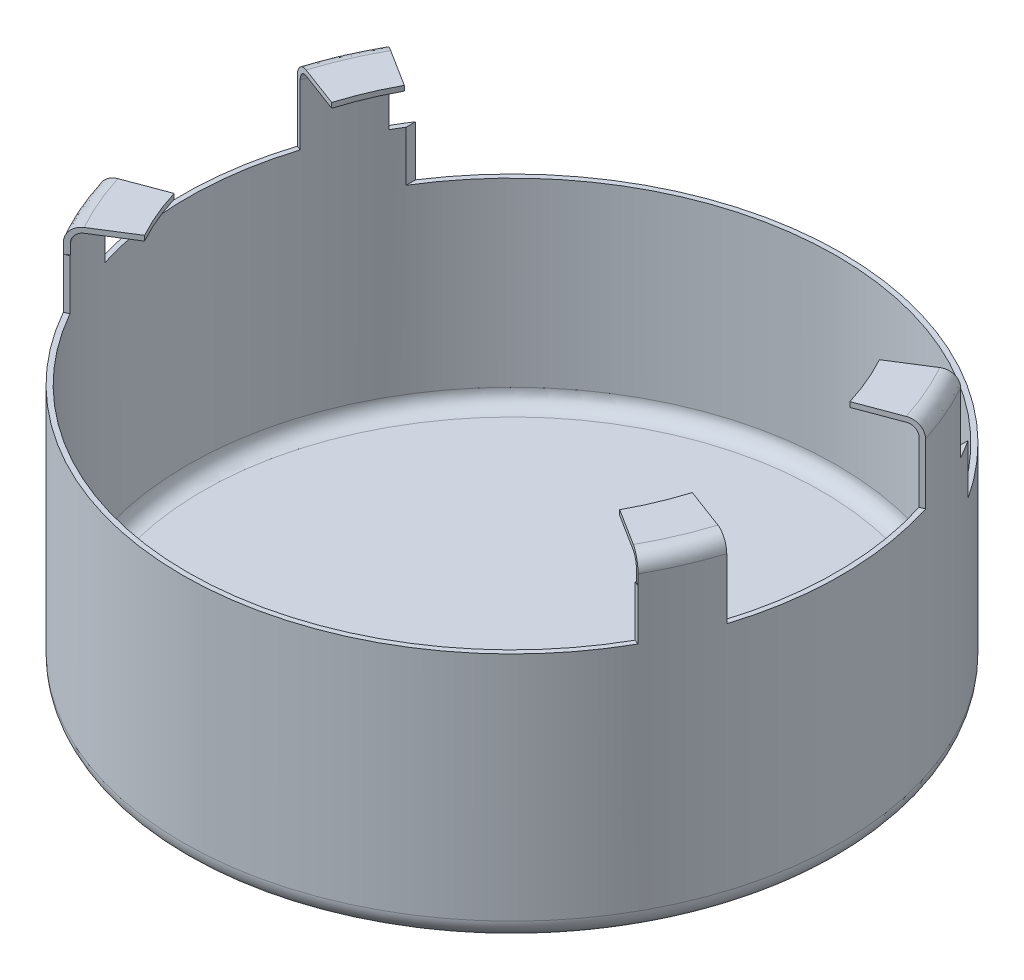
SolidWorks part; units mm, degrees
other "DetailItem6"
ref_plane "Front" through (0, 0, 0) normal (0, 0, 1) x (1, 0, 0)
ref_plane "Top" through (0, 0, 0) normal (0, 1, 0) x (1, 0, 0)
ref_plane "Right" through (0, 0, 0) normal (1, 0, 0) x (0, 0, -1)
sketch "Sketch1" plane through (0, 0, 0) normal (0, 1, 0) x (1, 0, 0)
  circle A0 centre (0, 0) radius 8.3185
extrude "Boss-Extrude1" add sketch "Sketch1" along normal blind 6.35
fillet "Fillet1" radius 0.508 1 edges at (0, 0, 8.3185)
shell "Shell1" thickness 0.127
sketch "Sketch11" plane through (0, 0, 0) normal (0, 0, 1) x (1, 0, 0)
  line L0 (8.3185, 6.35) -> (-8.3185, 6.35) construction
  line L1 (-6.9728, 5.08) -> (6.9728, 5.08)
  line L2 (-6.9728, 5.08) -> (-6.9728, 10.4572)
  line L3 (-6.9728, 10.4572) -> (6.9728, 10.4572)
  line L4 (6.9728, 5.08) -> (6.9728, 10.4572)
  line L5 (-6.9728, 5.08) -> (6.9728, 10.4572) construction
  line L6 (-6.9728, 10.4572) -> (6.9728, 5.08) construction
  point P0 (0, 7.7686)
  dimension "D1" = 1.27
extrude "Cut-Extrude1" cut sketch "Sketch11" against normal blind 9.144
sketch "Sketch12" plane through (0, 6.35, 0) normal (0, 1, 0) x (1, 0, 0)
  line L0 (0, 0) -> (0, 5.2829) construction
  line L1 (-7.1334, 4.0268) -> (-7.2538, 4.0718)
  line L2 (-7.8118, 2.465) -> (-7.9309, 2.5096)
  line L3 (0, 0) -> (4.1266, 0) construction
  line L4 (7.8118, 2.465) -> (7.9309, 2.5096)
  line L5 (7.1334, 4.0268) -> (7.2538, 4.0718)
  line L6 (7.1334, -4.0268) -> (7.2538, -4.0718)
  line L7 (7.8118, -2.465) -> (7.9309, -2.5096)
  line L8 (-7.8118, -2.465) -> (-7.9309, -2.5096)
  line L9 (-7.1334, -4.0268) -> (-7.2538, -4.0718)
  arc A0 (-6.9728, 4.5362) -> (6.9728, 4.5362) centre (0, 0) ccw construction
  arc A1 (-7.2538, 4.0718) -> (-7.9309, 2.5096) centre (0, 0) ccw
  circle A2 centre (0, 0) radius 8.1915 construction
  arc A3 (-7.1334, 4.0268) -> (-7.8118, 2.465) centre (0, 0) ccw
  arc A4 (7.1334, 4.0268) -> (7.8118, 2.465) centre (0, 0) cw
  arc A5 (7.2538, 4.0718) -> (7.9309, 2.5096) centre (0, 0) cw
  arc A6 (7.2538, -4.0718) -> (7.9309, -2.5096) centre (0, 0) ccw
  arc A7 (7.1334, -4.0268) -> (7.8118, -2.465) centre (0, 0) ccw
  arc A8 (-7.1334, -4.0268) -> (-7.8118, -2.465) centre (0, 0) cw
  arc A9 (-7.2538, -4.0718) -> (-7.9309, -2.5096) centre (0, 0) cw
extrude "Boss-Extrude2" add sketch "Sketch12" along normal blind 1.27
sketch "Sketch13" plane through (-0.151, 0, 0.4032) normal (-0.3506, 0, 0.9365) x (0.9365, 0, 0.3506)
  line L0 (-8.1802, 7.62) -> (-8.1802, 7.8808)
  line L1 (-7.9262, 8.1348) -> (-6.8225, 8.1348)
  line L2 (-6.8225, 8.1348) -> (-6.8225, 8.2618)
  line L3 (-6.8225, 8.2618) -> (-7.9264, 8.2618)
  line L4 (-8.3074, 7.62) -> (-8.3074, 7.8808)
  line L5 (-8.3074, 7.62) -> (-8.1802, 7.62)
  arc A0 (-8.1802, 7.8808) -> (-7.9262, 8.1348) centre (-7.9262, 7.8808) cw
  arc A1 (-8.3074, 7.8808) -> (-7.9264, 8.2618) centre (-7.9264, 7.8808) cw
  dimension "D1" = 0.254
  dimension "D2" = 0.381
  dimension "D3" = 0.127
sketch3d "3DSketch2"
  arc A0 (-7.2538, 7.62, -4.0718) -> (-7.9309, 7.62, -2.5096) centre (0, 7.62, 0) ccw construction
  arc A1 (-7.2538, 7.62, -4.0718) -> (-7.9309, 7.62, -2.5096) centre (0, 7.62, 0) ccw
  point P3 (0, 15.9385, 0)
  point P4 (0, 15.9385, 0)
sweep "Sweep1" add profiles "Sketch13" path "3DSketch2"
mirror "Mirror1" about plane through (0, 0, 0) normal (1, 0, 0) of "Sweep1"
mirror "Mirror2" about plane through (0, 0, 0) normal (0, 0, 1) of "Mirror1", "Sweep1"
sketch "Sketch14" plane through (0, 0, 0) normal (0, -1, 0) x (1, 0, 0)
  circle A0 centre (0, 0) radius 2.413
  circle A1 centre (0, 0) radius 2.3168
extrude "Cut-Extrude2" cut sketch "Sketch14" against normal blind 0.0254
sketch "Bend-Lines1" [suppressed] plane through (0, 0, 0) normal (0, 1, 0) x (1, 0, 0)
sketch "Bounding-Box1" [suppressed] plane through (0, 0, 0) normal (0, 1, 0) x (1, 0, 0)
